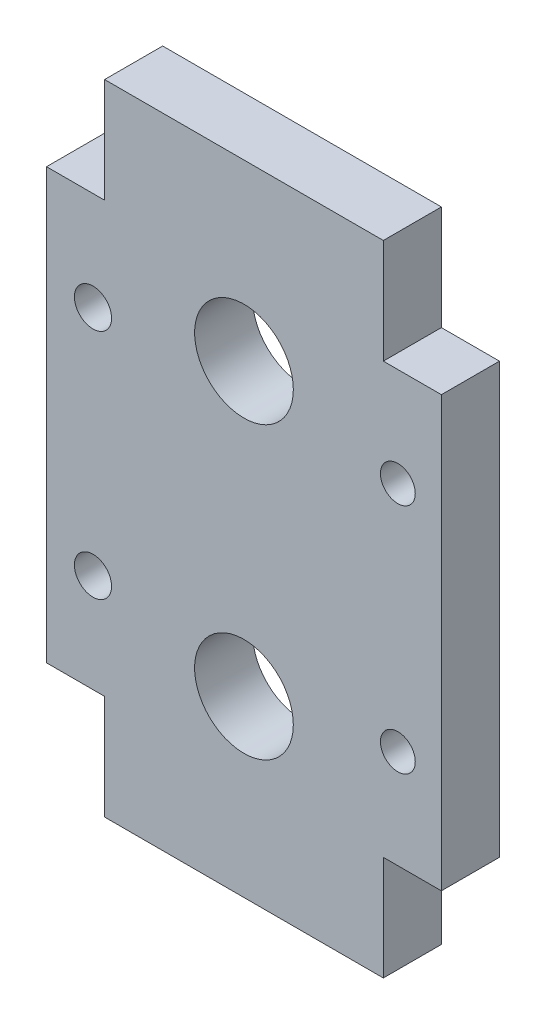
SolidWorks part; units mm, degrees
ref_plane "Front Plane" through (0, 0, 0) normal (0, 0, 1) x (1, 0, 0)
ref_plane "Top Plane" through (0, 0, 0) normal (0, 1, 0) x (1, 0, 0)
ref_plane "Right Plane" through (0, 0, 0) normal (1, 0, 0) x (0, 0, -1)
sketch "Sketch1" plane through (0, 0, 0) normal (0, 0, 1) x (1, 0, 0)
  line L30 (45.2509, -25.2077) -> (50.0009, -20.4577)
  line L31 (50.0009, -20.4577) -> (50.0009, 24.6887)
  line L32 (50.0009, 24.6887) -> (45.1474, 29.5423)
  line L33 (45.1474, 29.5423) -> (26.3545, 29.5423)
  line L34 (26.3545, 29.5423) -> (21.2509, 24.4387)
  line L35 (21.2509, 24.4387) -> (21.2509, 18.0423)
  line L36 (21.2509, 18.0423) -> (20.4081, 18.0423)
  line L37 (20.4081, 18.0423) -> (16.7009, 18.0423)
  line L38 (-5.4991, 12.0433) -> (-5.4991, 12.0391)
  line L39 (-5.4991, -7.4545) -> (-5.4991, -7.4587)
  line L40 (16.7009, -13.4577) -> (20.4081, -13.4577)
  line L41 (20.4081, -13.4577) -> (21.2509, -13.4577)
  line L42 (21.2509, -13.4577) -> (21.2509, -20.2077)
  line L43 (21.2509, -20.2077) -> (26.2509, -25.2077)
  line L44 (26.2509, -25.2077) -> (45.2509, -25.2077)
  arc A10 (16.7009, 18.0423) -> (9.3423, 16.0756) centre (16.7009, 3.2923) ccw
  arc A11 (-5.4991, 12.0433) -> (9.3423, 16.0756) centre (-5.7491, 42.2923) ccw
  arc A12 (-5.4991, 12.0391) -> (-5.4991, -7.4545) centre (-5.7491, 2.2923) ccw
  arc A13 (9.3423, -11.491) -> (-5.4991, -7.4587) centre (-5.7491, -37.7077) ccw
  arc A14 (9.3423, -11.491) -> (16.7009, -13.4577) centre (16.7009, 1.2923) ccw
  circle A25 centre (46.7509, -7.7077) radius 1.5
  circle A26 centre (46.7509, 12.2923) radius 1.5
  circle A27 centre (33.5009, 14.7923) radius 4.25
  circle A28 centre (33.5009, -10.2077) radius 4.25
  circle A29 centre (19.2509, 12.2923) radius 1.5
  circle A30 centre (19.2509, -7.7077) radius 1.5
  circle B0 centre (-5.7491, 2.2923) radius 5
  circle B1 centre (1.2509, 2.3547) radius 1
  circle B2 centre (-5.6866, -4.7077) radius 1
  circle B3 centre (-12.7491, 2.2298) radius 1
  circle B4 centre (-5.8115, 9.2923) radius 1
  dimension "D2" = 8.5
  dimension "D3" = 3
  dimension "D4" = 14.75
  dimension "D5" = 30.25
  dimension "D6" = 9.75
  dimension "D8" = 9.3423
  dimension "D9" = 16.7009
  dimension "D10" = 19.2509
  dimension "D11" = 20.4081
  dimension "D12" = 21.2509
  dimension "D13" = 26.2509
  dimension "D14" = 26.3545
  dimension "D15" = 33.5009
  dimension "D16" = 45.1474
  dimension "D17" = 45.2509
  dimension "D18" = 46.7509
  dimension "D19" = 50.0009
  dimension "D20" = 5.4991
  dimension "D22" = 1.2923
  dimension "D26" = 2.2923
  dimension "D28" = 24.4387
  dimension "D30" = 24.6887
  dimension "D31" = 20.2077
  dimension "D32" = 12.2923
  dimension "D33" = 14.7923
  dimension "D43" = 7.7077
  dimension "D44" = 10.2077
sketch_block_instance "Block1-1"
sketch_block "Block1" parameters "D1"=2, "D2"=10
extrude "Boss-Extrude2" add sketch "Sketch1" along normal blind 5
sketch "Sketch2" plane through (0, 0, 0) normal (0, 0, -1) x (-1, 0, 0)
  line L0 (-26.2509, -25.2077) -> (-21.5009, -25.2077)
  line L1 (-21.5009, -25.2077) -> (-21.5009, -20.4577)
  line L2 (-21.5009, -16.2077) -> (-21.5009, -25.2077) construction
  line L3 (-21.2509, -20.2077) -> (-26.2509, -25.2077) construction
  line L4 (-21.5009, -20.4577) -> (-26.2509, -25.2077)
  line L5 (-45.2509, -25.2077) -> (-45.5009, -25.2077)
  line L6 (-45.5009, -25.2077) -> (-45.5009, -24.9577)
  line L7 (-45.2509, -25.2077) -> (-50.0009, -20.4577) construction
  line L8 (-45.5009, -25.2077) -> (-45.5009, -16.2077) construction
  line L9 (-45.5009, -24.9577) -> (-45.2509, -25.2077)
  line L10 (-45.5009, 29.1887) -> (-45.5009, 29.7923)
  line L11 (-50.0009, 24.6887) -> (-45.1474, 29.5423) construction
  line L12 (-45.5009, 20.7923) -> (-45.5009, 29.7923) construction
  line L13 (-45.5009, 29.7923) -> (-21.5009, 29.7923)
  line L14 (-21.5009, 29.7923) -> (-21.5009, 24.6887)
  line L15 (-26.3545, 29.5423) -> (-21.2509, 24.4387) construction
  line L16 (-21.5009, 29.7923) -> (-21.5009, 20.7923) construction
  line L17 (-21.5009, 24.6887) -> (-26.3545, 29.5423)
  line L18 (-26.3545, 29.5423) -> (-45.1474, 29.5423)
  line L19 (-45.1474, 29.5423) -> (-45.5009, 29.1887)
  line L20 (-50.5009, 20.7923) -> (-50.0009, 20.7923)
  line L21 (-50.0009, -20.4577) -> (-50.0009, 24.6887) construction
  line L22 (-50.5009, 20.7923) -> (-45.5009, 20.7923) construction
  line L23 (-50.0009, 20.7923) -> (-50.0009, -16.2077)
  line L24 (-45.5009, -16.2077) -> (-50.5009, -16.2077) construction
  line L25 (-50.0009, -16.2077) -> (-50.5009, -16.2077)
  line L26 (-50.5009, -16.2077) -> (-50.5009, 20.7923)
extrude "Boss-Extrude3" add sketch "Sketch2" against normal up to vertex (5 mm away)
sketch "Sketch3" plane through (0, 0, 0) normal (0, 0, -1) x (-1, 0, 0)
  line L0 (-50.0009, -16.2077) -> (-45.5009, -16.2077)
  line L1 (-45.5009, -16.2077) -> (-45.5009, -25.2077)
  line L2 (-45.5009, -25.2077) -> (-50.0009, -20.4577)
  line L3 (-50.0009, -20.4577) -> (-50.0009, -16.2077)
  line L4 (-50.5009, 20.7923) -> (-45.5009, 20.7923)
  line L5 (-45.5009, 20.7923) -> (-45.5009, 29.1887)
  line L6 (-45.5009, 29.1887) -> (-50.0009, 24.6887)
  line L7 (-50.0009, 24.6887) -> (-50.5009, 20.7923)
  line L8 (-21.5009, -16.2077) -> (-21.5009, -20.4577)
  line L9 (-21.5009, -20.4577) -> (-21.2509, -20.2077)
  line L10 (-21.2509, -20.2077) -> (-21.2509, -16.2077)
  line L11 (-21.2509, -13.4577) -> (-21.2509, -20.2077) construction
  line L12 (-16.5009, -16.2077) -> (-21.5009, -16.2077) construction
  line L13 (-21.2509, -16.2077) -> (-21.5009, -16.2077)
  line L14 (-21.5009, 20.7923) -> (-21.2509, 20.7923)
  line L15 (-21.2509, 24.4387) -> (-21.2509, 18.0423) construction
  line L16 (-21.5009, 20.7923) -> (-16.5009, 20.7923) construction
  line L17 (-21.2509, 20.7923) -> (-21.2509, 24.4387)
  line L18 (-21.2509, 24.4387) -> (-21.5009, 24.6887)
  line L19 (-21.5009, 24.6887) -> (-21.5009, 20.7923)
extrude "Cut-Extrude1" cut sketch "Sketch3" against normal blind 10
sketch "Sketch4" plane through (0, 0, 0) normal (0, 0, -1) x (-1, 0, 0)
  line L0 (-21.2509, 20.7923) -> (-16.5009, 20.7923)
  line L1 (-16.5009, 20.7923) -> (-16.5009, 18.0409)
  line L2 (-16.5009, 20.7923) -> (-16.5009, -16.2077) construction
  line L3 (-21.2509, 20.7923) -> (-21.2509, 18.0423)
  line L4 (-21.2509, 18.0423) -> (-16.7009, 18.0423)
  line L5 (-16.5009, -13.4564) -> (-16.5009, -16.2077)
  line L6 (-16.5009, -16.2077) -> (-21.2509, -16.2077)
  line L7 (-21.2509, -16.2077) -> (-21.2509, -13.4577)
  line L8 (-21.2509, -13.4577) -> (-16.7009, -13.4577)
  arc A0 (-9.3423, 16.0756) -> (-16.7009, 18.0423) centre (-16.7009, 3.2923) ccw construction
  arc A1 (-16.5009, 18.0409) -> (-16.7009, 18.0423) centre (-16.7009, 3.2923) ccw
  arc A2 (-16.7009, -13.4577) -> (-16.5009, -13.4564) centre (-16.7009, 1.2923) ccw
  arc A3 (-16.7009, -13.4577) -> (-9.3423, -11.491) centre (-16.7009, 1.2923) ccw construction
extrude "Boss-Extrude4" add sketch "Sketch4" against normal up to vertex (5 mm away)
sketch "Sketch5" plane through (0, 0, 5) normal (0, 0, 1) x (1, 0, 0)
  circle A0 centre (20.5009, -7.7077) radius 1.6
  circle A1 centre (20.5009, 12.2923) radius 1.6
  circle A2 centre (20.5009, -7.7077) radius 2.1 construction
  circle A3 centre (20.5009, 12.2923) radius 2.1 construction
  dimension "D1" = 3.2
  dimension "D2" = 3.2
extrude "Cut-Extrude2" cut sketch "Sketch5" against normal blind 10
sketch "Sketch6" plane through (0, 0, 5) normal (0, 0, 1) x (1, 0, 0)
  arc A0 (19.7519, -6.2938) -> (19.7519, -9.1216) centre (20.5009, -7.7077) ccw
  arc A1 (19.7519, -6.2938) -> (19.7519, -9.1216) centre (19.2509, -7.7077) ccw
  arc A2 (19.7519, 13.7062) -> (19.7519, 10.8784) centre (20.5009, 12.2923) ccw
  arc A3 (19.7519, 13.7062) -> (19.7519, 10.8784) centre (19.2509, 12.2923) ccw
extrude "Boss-Extrude5" add sketch "Sketch6" against normal up to vertex (5 mm away)
sketch "Sketch7" plane through (0, 0, 0) normal (0, 0, -1) x (-1, 0, 0)
  circle A0 centre (-1.2509, 2.3547) radius 1
  circle A1 centre (12.7491, 2.2298) radius 1
extrude "Boss-Extrude6" add sketch "Sketch7" against normal up to vertex (5 mm away)
sketch "Sketch8" plane through (16.5009, 0, 0) normal (-1, 0, 0) x (0, 0, 1)
  line L0 (5, -16.2077) -> (5, 20.7923)
  line L1 (5, -16.2077) -> (0, -16.2077)
  line L2 (5, 20.7923) -> (0, 20.7923)
  line L3 (0, -16.2077) -> (0, 20.7923)
  line L4 (0, 18.0409) -> (0, 20.7923) construction
extrude "Cut-Extrude3" cut sketch "Sketch8" along normal through all
